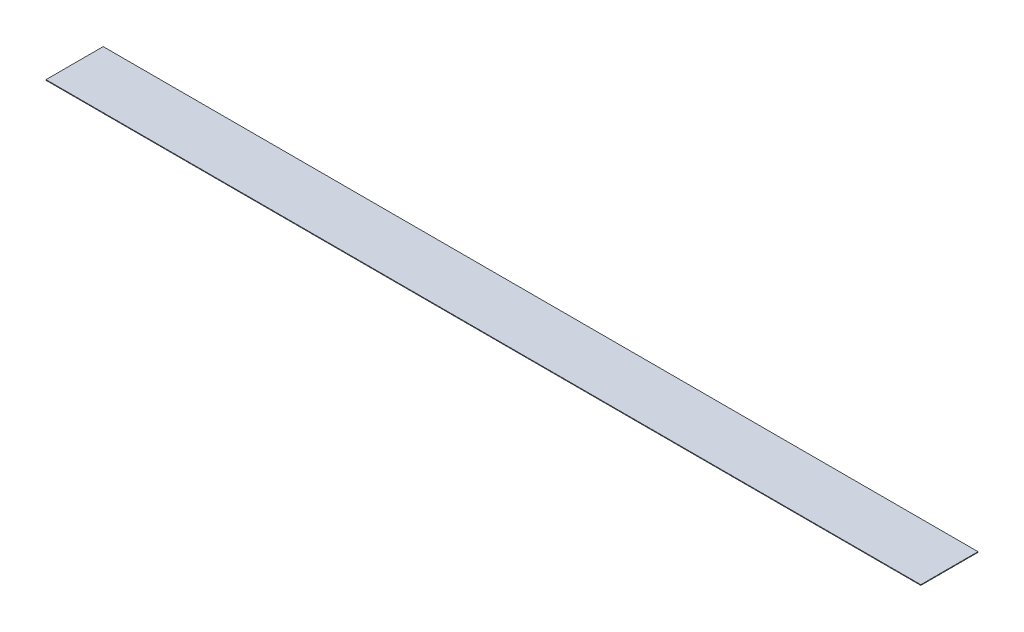
SolidWorks part; units mm, degrees
ref_plane "Front" through (0, 0, 0) normal (0, 0, 1) x (1, 0, 0)
ref_plane "Top" through (0, 0, 0) normal (0, 1, 0) x (1, 0, 0)
ref_plane "Right" through (0, 0, 0) normal (1, 0, 0) x (0, 0, -1)
sketch "Sketch1" plane through (0, 0, 0) normal (0, 1, 0) x (1, 0, 0)
  line L1 (0, 34.78) -> (1064, 34.78)
  line L2 (0, 34.78) -> (0, -34.78)
  line L3 (0, -34.78) -> (1064, -34.78)
  line L4 (1064, 34.78) -> (1064, -34.78)
  dimension "D1" = 69.56
  dimension "D2" = 1064
extrude "Extrude1" add sketch "Sketch1" along normal blind 0.762
